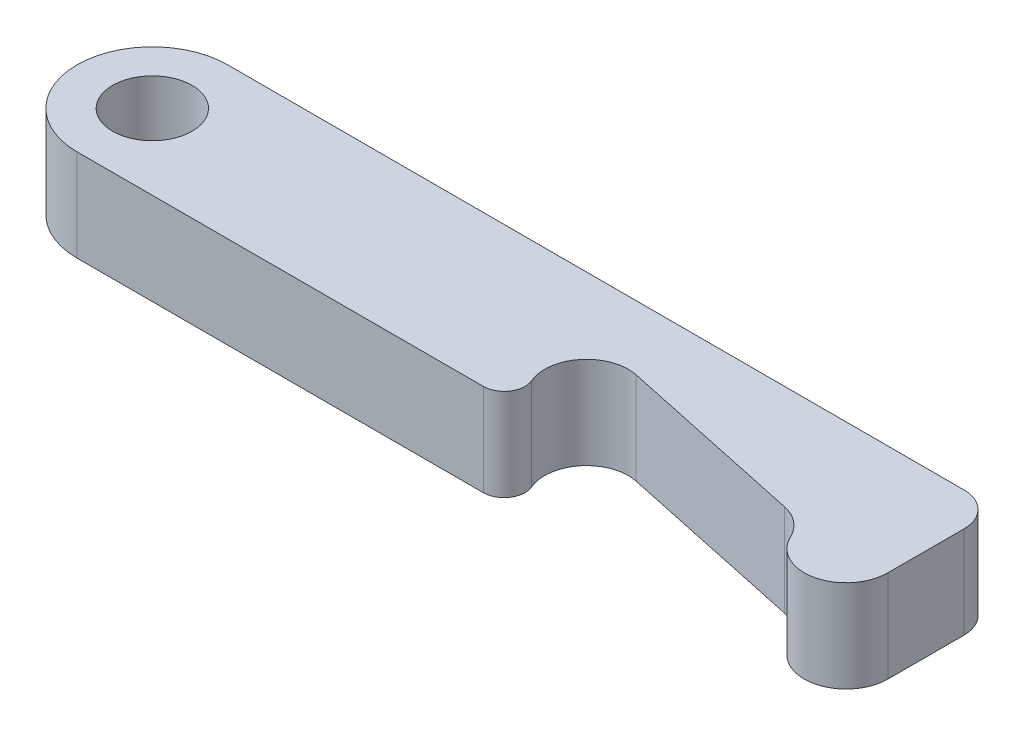
SolidWorks part; units mm, degrees
ref_plane "Front Plane" through (0, 0, 0) normal (0, 0, 1) x (1, 0, 0)
ref_plane "Top Plane" through (0, 0, 0) normal (0, 1, 0) x (1, 0, 0)
ref_plane "Right Plane" through (0, 0, 0) normal (1, 0, 0) x (0, 0, -1)
sketch "Sketch1" plane through (0, 0, 0) normal (0, 1, 0) x (1, 0, 0)
  line L0 (0, 9) -> (0, -9) construction
  line L1 (0, 9) -> (88, 9)
  line L2 (92, 5) -> (92, -4.1188)
  line L3 (78.9784, -3.4582) -> (56.4784, 1.3243)
  line L4 (0, -9) -> (48.5363, -9)
  line L5 (48.5363, -6.5) -> (48.5363, -9) construction
  line L6 (50.8371, -5.5222) -> (48.5363, -6.5) construction
  arc A0 (0, -9) -> (0, 9) centre (0, 0) cw
  arc A1 (88, 9) -> (92, 5) centre (88, 5) cw
  arc A2 (92, -4.1188) -> (82.4694, -6.2339) centre (87, -4.1188) cw
  arc A3 (82.4694, -6.2339) -> (78.9784, -3.4582) centre (77.9388, -8.349) ccw
  arc A4 (56.4784, 1.3243) -> (50.8371, -5.5222) centre (55.4388, -3.5665) ccw
  arc A5 (50.8371, -5.5222) -> (48.5363, -9) centre (48.5363, -6.5) cw
  circle A6 centre (0, 0) radius 4.75
  point P17 (-9, 0)
  point P18 (88.0833, -9)
  point P19 (56.4784, 1.3243)
  dimension "D2" = 4
  dimension "D3" = 5
  dimension "D4" = 5
  dimension "D5" = 2.5
  dimension "D6" = 5
  dimension "D9" = 9.5
  dimension "D1" = 18
  dimension "D7" = 22.5
  dimension "D8" = 12
  dimension "D10" = 0
  dimension "D11" = 101
extrude "Boss-Extrude1" add sketch "Sketch1" along normal blind 11
equation "\"B\"= 11"
equation "\"A\"= 101"
equation "\"D11@Sketch1\"=\"A\""
equation "\"D1@Boss-Extrude1\"=\"B\""
